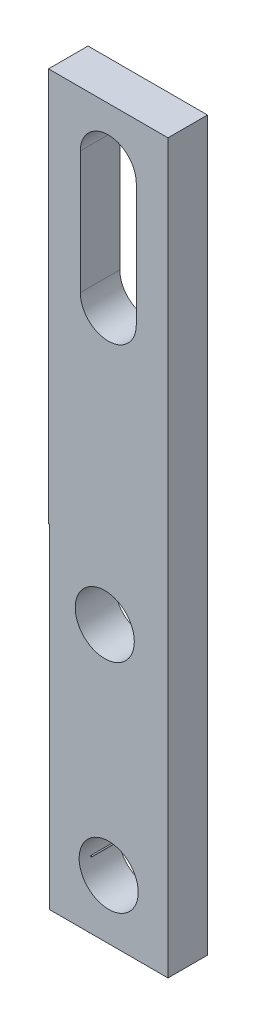
SolidWorks part; units mm, degrees
ref_plane "Front Plane" through (0, 0, 0) normal (0, 0, 1) x (1, 0, 0)
ref_plane "Top Plane" through (0, 0, 0) normal (0, 1, 0) x (1, 0, 0)
ref_plane "Right Plane" through (0, 0, 0) normal (1, 0, 0) x (0, 0, -1)
sketch "Sketch2" plane through (0, 0, 0) normal (0, 0, 1) x (1, 0, 0)
  circle A0 centre (-28.0323, -98.6169) radius 0.0397
  circle A1 centre (-27.1548, -85.2774) radius 1.8986
  circle A3 centre (0, 0) radius 2.3565
  circle A4 centre (-26.9016, -99.1074) radius 1.8987
  dimension "D1" = 3.7973
  dimension "D2" = 3.7973
  dimension "D3" = 13.83
sketch "Sketch3" plane through (0, 0, 0) normal (0, 0, 1) x (1, 0, 0)
  line L1 (-30.7116, -102.9174) -> (-23.0916, -102.9174)
  line L2 (-30.7116, -102.9174) -> (-30.7116, -81.4674)
  line L3 (-30.7116, -81.4674) -> (-23.0916, -81.4674)
  line L4 (-23.0916, -102.9174) -> (-23.0916, -81.4674)
  line L5 (-30.7702, -81.4674) -> (-23.0916, -81.4674)
  line L6 (-30.7702, -81.4674) -> (-30.7702, -56.1538)
  line L7 (-30.7702, -56.1538) -> (-23.0916, -56.1538)
  line L8 (-23.0916, -81.4674) -> (-23.0916, -56.1538)
  dimension "D1" = 3.81
  dimension "D2" = 3.81
  dimension "D3" = 3.81
  dimension "D4" = 3.81
  dimension "D5" = 25.3135
extrude "Boss-Extrude1" add sketch "Sketch3" along normal blind 2.54
extrude "Cut-Extrude1" cut sketch "Sketch2" along normal blind 4.572
sketch "Sketch4" plane through (0, 0, 2.54) normal (0, 0, 1) x (1, 0, 0)
  line L0 (-26.9309, -56.1538) -> (-26.9016, -102.9174) construction
  line L1 (-30.7702, -56.1538) -> (-23.0916, -56.1538) construction
  line L2 (-30.7116, -102.9174) -> (-23.0916, -102.9174) construction
  line L5 (-28.7287, -59.7074) -> (-28.7287, -67.5888)
  line L7 (-25.1287, -59.7074) -> (-25.1287, -67.5888)
  arc A3 (-28.7287, -67.5888) -> (-25.1287, -67.5888) centre (-26.9287, -67.5888) ccw
  arc A4 (-28.7287, -59.7074) -> (-25.1287, -59.7074) centre (-26.9287, -59.7074) cw
extrude "Cut-Extrude2" cut sketch "Sketch4" against normal blind 2.54
